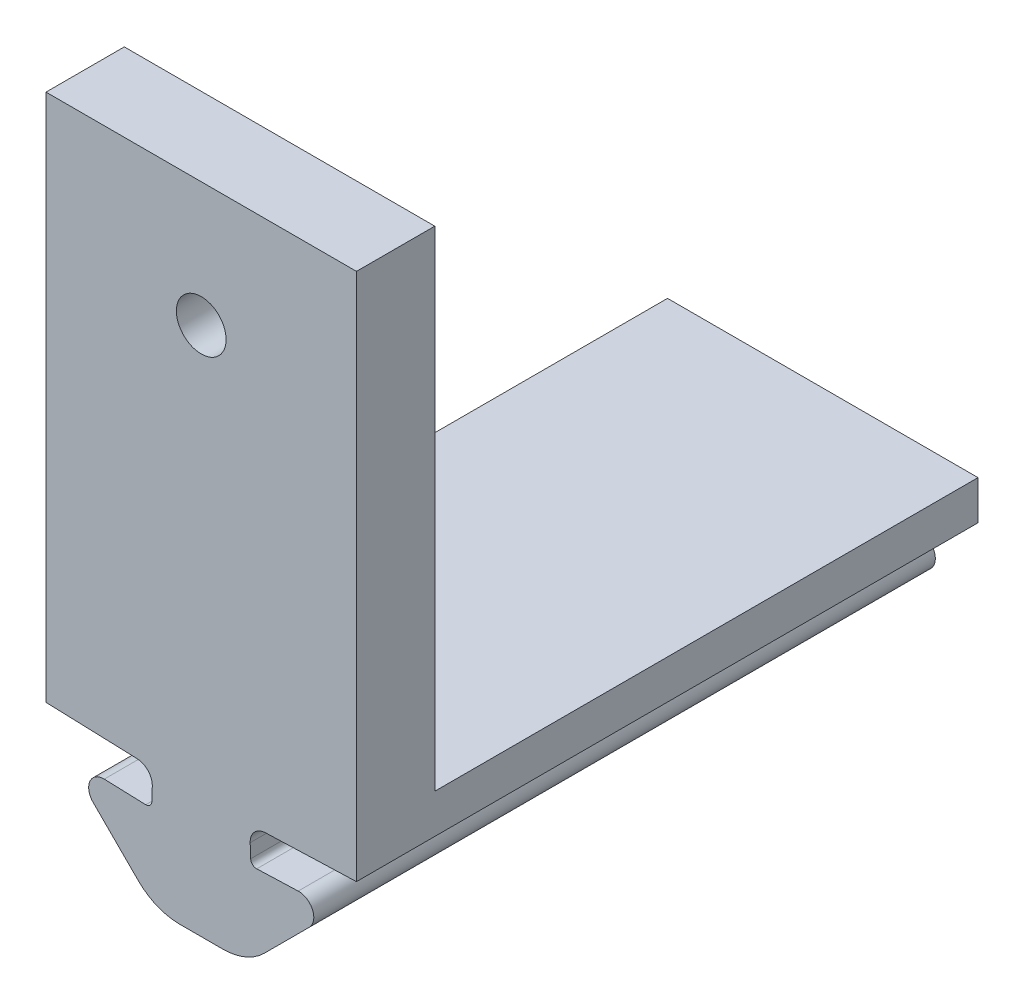
SolidWorks part; units mm, degrees
ref_plane "Front Plane" through (0, 0, 0) normal (0, 0, 1) x (1, 0, 0)
ref_plane "Top Plane" through (0, 0, 0) normal (0, 1, 0) x (1, 0, 0)
ref_plane "Right Plane" through (0, 0, 0) normal (1, 0, 0) x (0, 0, -1)
sketch "Sketch2" plane through (0, 0, 0) normal (0, 0, 1) x (1, 0, 0)
  line L1 (-50.3756, 45.6099) -> (-50.3512, 46.3094)
  line L2 (-50.6859, 45.3205) -> (-52.8037, 45.3945)
  line L6 (-55.7809, 47.2995) -> (-51.1228, 47.1369)
  line L7 (-51.0743, 41.7794) -> (-53.3751, 44.0803)
  line L8 (-47.8507, 40.9008) -> (-48.9529, 40.9008)
  line L9 (-47.8507, 40.9008) -> (-47.8507, 47.2995)
  line L10 (-47.8507, 47.2995) -> (-55.7809, 47.2995)
  arc A0 (-50.6859, 45.3205) -> (-50.3756, 45.6099) centre (-50.6754, 45.6203) ccw
  arc A7 (-50.3512, 46.3094) -> (-51.1228, 47.1369) centre (-51.1507, 46.3374) ccw
  arc A8 (-52.8037, 45.3945) -> (-53.3751, 44.0803) centre (-52.8306, 44.6248) ccw
  arc A9 (-51.0743, 41.7794) -> (-48.9529, 40.9008) centre (-48.9529, 43.9008) ccw
extrude "Boss-Extrude1" add sketch "Sketch2" along normal blind 31.75
ref_plane "Plane2" through (0, 0, 0) normal (0.7071, -0.7071, 0) x (-0.7071, -0.7071, 0)
ref_plane "Plane3" through (-42.746, 42.746, 0) normal (0.7071, -0.7071, 0) x (-0.7071, -0.7071, 0)
mirror "Mirror2" about plane through (-47.8507, 40.9008, 31.75) normal (-1, 0, 0) of "Boss-Extrude1"
ref_plane "Plane7" through (0, 47.2995, 0) normal (0, 1, 0) x (1, 0, 0)
sketch "Sketch19" plane through (0, 47.2995, 0) normal (0, 1, 0) x (1, 0, 0)
  line L0 (-55.7809, -31.75) -> (-55.7809, 0) construction
  line L1 (-55.7809, 0) -> (-39.9205, 0)
  line L2 (-55.7809, 0) -> (-55.7809, -31.75)
  line L3 (-55.7809, -31.75) -> (-39.9205, -31.75)
  line L4 (-39.9205, 0) -> (-39.9205, -31.75)
  line L5 (-39.9205, -31.75) -> (-39.9205, 0) construction
  line L6 (-39.9205, 0) -> (-55.7809, 0) construction
  dimension "D1" = 0
  dimension "D2" = 31.75
extrude "Boss-Extrude7" add sketch "Sketch19" along normal blind 2
sketch "Sketch23" plane through (0, 49.2995, 0) normal (0, 1, 0) x (1, 0, 0)
  line L0 (-55.7809, 0) -> (-55.7809, -31.75) construction
  line L1 (-55.7809, -27.75) -> (-39.9205, -27.75)
  line L2 (-55.7809, -27.75) -> (-55.7809, -31.75)
  line L3 (-55.7809, -31.75) -> (-39.9205, -31.75)
  line L4 (-39.9205, -27.75) -> (-39.9205, -31.75)
  line L5 (-39.9205, -31.75) -> (-39.9205, 0) construction
  line L8 (-55.7809, -31.75) -> (-39.9205, -31.75) construction
  dimension "D1" = 0
  dimension "D2" = 0
  dimension "D3" = 0
  dimension "D4" = 4
extrude "Boss-Extrude8" add sketch "Sketch23" along normal blind 25
ref_plane "Plane8" through (-39.9205, 49.2995, 27.75) normal (0, -1, 0) x (-1, 0, 0)
sketch "Sketch24" plane through (0, 0, 27.75) normal (0, 0, -1) x (-1, 0, 0)
  line L0 (39.9205, 74.2995) -> (55.7809, 74.2995) construction
  line L5 (47.8507, 74.2995) -> (47.8507, 61.5995) construction
  circle A1 centre (47.8507, 67.9495) radius 1.27
  dimension "D1" = 6.35
  dimension "D4" = 2.54
extrude "Cut-Extrude1" cut sketch "Sketch24" against normal through all
